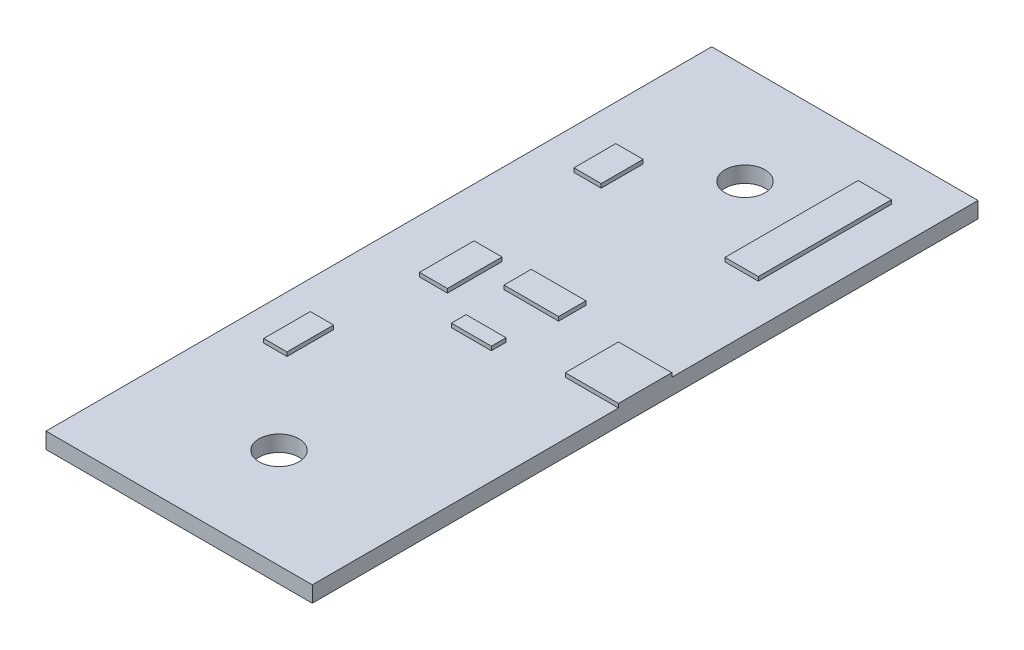
SolidWorks part; units mm, degrees
ref_plane "Front Plane" through (0, 0, 0) normal (0, 0, 1) x (1, 0, 0)
ref_plane "Top Plane" through (0, 0, 0) normal (0, 1, 0) x (1, 0, 0)
ref_plane "Right Plane" through (0, 0, 0) normal (1, 0, 0) x (0, 0, -1)
sketch "Sketch1" plane through (0, 0, 0) normal (0, 1, 0) x (1, 0, 0)
  line L1 (-10, -25) -> (10, -25)
  line L2 (-10, -25) -> (-10, 25)
  line L3 (-10, 25) -> (10, 25)
  line L4 (10, -25) -> (10, 25)
  line L5 (-10, -25) -> (10, 25) construction
  line L6 (-10, 25) -> (10, -25) construction
  point P0 (0, 0)
  dimension "D1" = 50
  dimension "D2" = 20
extrude "Boss-Extrude1" add sketch "Sketch1" along normal blind 1.2
sketch "Sketch2" plane through (0, 0, 0) normal (0, -1, 0) x (1, 0, 0)
  line L0 (-10, 0) -> (10, 0) construction
  line L1 (-10, -25) -> (-10, 25) construction
  line L2 (10, 25) -> (10, -25) construction
  line L3 (-10, 25) -> (10, 25) construction
  line L4 (0, 0) -> (0, 17.5) construction
  circle A0 centre (0, 17.5) radius 1.5
  circle A1 centre (0, -17.5) radius 1.5
  dimension "D2" = 3
  dimension "D1" = 7.5
extrude "Cut-Extrude1" cut sketch "Sketch2" against normal through all
sketch "Sketch3" plane through (0, 0, 0) normal (0, -1, 0) x (1, 0, 0)
  line L0 (10, 25) -> (10, -25) construction
  line L1 (4.5, -21.5) -> (7, -21.5)
  line L2 (4.5, -21.5) -> (4.5, -11.5)
  line L3 (4.5, -11.5) -> (7, -11.5)
  line L4 (7, -21.5) -> (7, -11.5)
  line L5 (-7, -14.8) -> (-4.95, -14.8)
  line L6 (-7, -14.8) -> (-7, -11.65)
  line L7 (-7, -11.65) -> (-4.95, -11.65)
  line L8 (-4.95, -14.8) -> (-4.95, -11.65)
  line L9 (-6, 0.95) -> (-3.9, 0.95)
  line L10 (-6, 0.95) -> (-6, -3.15)
  line L11 (-6, -3.15) -> (-3.9, -3.15)
  line L12 (-3.9, 0.95) -> (-3.9, -3.15)
  line L13 (-2, -1.4) -> (2.1, -1.4)
  line L14 (-2, -1.4) -> (-2, -3.45)
  line L15 (-2, -3.45) -> (2.1, -3.45)
  line L16 (2.1, -1.4) -> (2.1, -3.45)
  line L17 (-1.5, 3.05) -> (1.5, 3.05)
  line L18 (-1.5, 3.05) -> (-1.5, 1.95)
  line L19 (-1.5, 1.95) -> (1.5, 1.95)
  line L20 (1.5, 3.05) -> (1.5, 1.95)
  line L21 (10, 2) -> (6, 2)
  line L22 (10, 2) -> (10, -2)
  line L23 (10, -2) -> (6, -2)
  line L24 (6, 2) -> (6, -2)
  line L25 (10, -25) -> (-10, -25) construction
  line L26 (-7.55, 11.1) -> (-5.8, 11.1)
  line L27 (-7.55, 11.1) -> (-7.55, 7.6)
  line L28 (-7.55, 7.6) -> (-5.8, 7.6)
  line L29 (-5.8, 11.1) -> (-5.8, 7.6)
  line L30 (-10, -25) -> (-10, 25) construction
  line L31 (-10, 25) -> (10, 25) construction
  point P34 (6, 0)
  dimension "D1" = 3.5
  dimension "D3" = 3
  dimension "D4" = 2.5
  dimension "D5" = 10.2
  dimension "D6" = 3.15
  dimension "D7" = 3
  dimension "D8" = 2.05
  dimension "D9" = 2.45
  dimension "D10" = 1.75
  dimension "D11" = 4
  dimension "D12" = 2.1
  dimension "D13" = 8
  dimension "D14" = 4.1
  dimension "D15" = 4
  dimension "D16" = 8.5
  dimension "D17" = 3
  dimension "D18" = 4
  dimension "D19" = 13.9
  dimension "D20" = 3.5
  dimension "D21" = 21.95
  dimension "D22" = 1.1
  dimension "D23" = 21.85
  dimension "D24" = 4.1
  dimension "D25" = 21.55
  dimension "D26" = 2.05
  dimension "D27" = 13.5
extrude "Boss-Extrude2" add sketch "Sketch3" against normal blind 1.5
